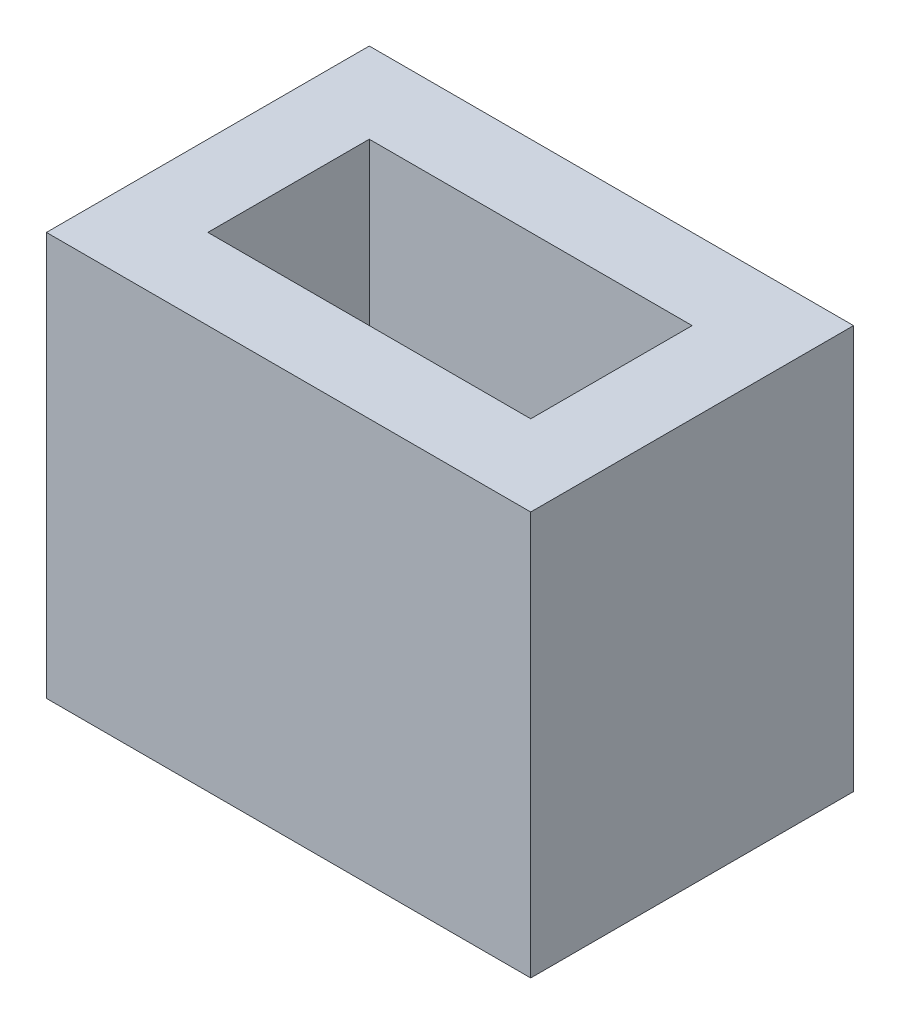
SolidWorks part; units mm, degrees
ref_plane "前视基准面" through (0, 0, 0) normal (0, 0, 1) x (1, 0, 0)
ref_plane "上视基准面" through (0, 0, 0) normal (0, 1, 0) x (1, 0, 0)
ref_plane "右视基准面" through (0, 0, 0) normal (1, 0, 0) x (0, 0, -1)
sketch "草图1" plane through (0, 0, 0) normal (0, 1, 0) x (1, 0, 0)
  line L1 (-4, 2) -> (4, 2)
  line L2 (-4, 2) -> (-4, -2)
  line L3 (-4, -2) -> (4, -2)
  line L4 (4, 2) -> (4, -2)
  line L5 (-4, 2) -> (4, -2) construction
  line L6 (-4, -2) -> (4, 2) construction
  line L7 (-6, 4) -> (6, 4)
  line L8 (-6, 4) -> (-6, -4)
  line L9 (-6, -4) -> (6, -4)
  line L10 (6, 4) -> (6, -4)
  line L11 (-6, 4) -> (6, -4) construction
  line L12 (-6, -4) -> (6, 4) construction
  point P0 (0, 0)
  point P6 (0, 0)
  dimension "D1" = 4
  dimension "D2" = 8
  dimension "D3" = 12
  dimension "D4" = 8
extrude "凸台-拉伸1" add sketch "草图1" along normal blind 10
